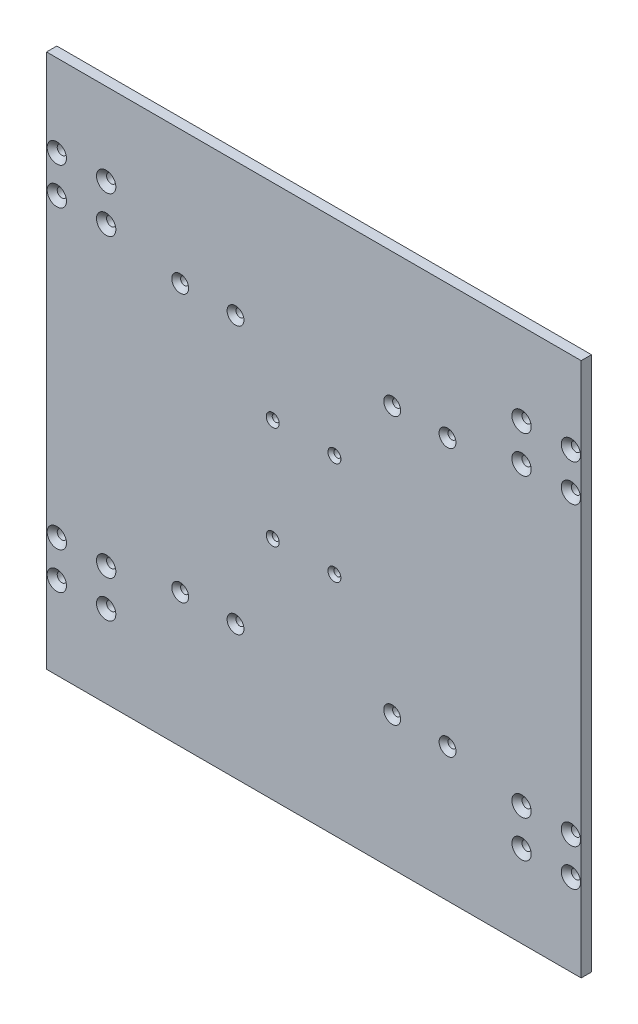
SolidWorks part; units mm, degrees
ref_plane "Front Plane" through (0, 0, 0) normal (0, 0, 1) x (1, 0, 0)
ref_plane "Top Plane" through (0, 0, 0) normal (0, 1, 0) x (1, 0, 0)
ref_plane "Right Plane" through (0, 0, 0) normal (1, 0, 0) x (0, 0, -1)
sketch "Sketch1" plane through (0, 0, 0) normal (0, 0, 1) x (1, 0, 0)
  line L1 (0, 0) -> (-260, 0)
  line L2 (0, 0) -> (0, 260)
  line L3 (0, 260) -> (-260, 260)
  line L4 (-260, 0) -> (-260, 260)
  dimension "D2" = 260
extrude "Boss-Extrude1" add sketch "Sketch1" along normal blind 5
sketch "Sketch3" plane through (0, 0, 0) normal (0, 0, -1) x (-1, 0, 0)
  line L0 (260, 260) -> (260, 0) construction
  line L1 (0, 260) -> (260, 260) construction
  circle A0 centre (135, 135) radius 1.5
  dimension "D1" = 3
  dimension "D3" = 125
  dimension "D2" = 125
extrude "temp. sensor" cut sketch "Sketch3" against normal blind 2
hole_wizard "CSK for M4 Flat Head Machine Screw1" positions "Sketch5" profile "Sketch4" countersink size "M4" standard "ANSI Metric" end condition through all
sketch "Sketch5" plane through (0, 0, 5) normal (0, 0, 1) x (1, 0, 0)
  line L0 (-260, 260) -> (-260, 0) construction
  line L1 (0, 260) -> (-260, 260) construction
  line L2 (-130, 260) -> (-130, 0) construction
  line L3 (-260, 0) -> (0, 0) construction
  line L5 (-260, 130) -> (0, 130) construction
  line L6 (0, 0) -> (0, 260) construction
  point P0 (-255, 220)
  point P2 (-231, 220)
  point P4 (-231, 202)
  point P6 (-255, 202)
  point P29 (-5, 202)
  point P30 (-29, 202)
  point P31 (-29, 220)
  point P32 (-5, 220)
  point P33 (-29, 58)
  point P34 (-5, 58)
  point P35 (-5, 40)
  point P36 (-29, 40)
  point P37 (-255, 40)
  point P38 (-231, 40)
  point P39 (-231, 58)
  point P40 (-255, 58)
  dimension "D1" = 5
  dimension "D2" = 24
  dimension "D3" = 40
  dimension "D4" = 18
sketch "Sketch4" plane through (-255, 220, 5) normal (1, 0, 0) x (0, -1, 0)
  line L0 (0, 0) -> (0, 5)
  line L1 (0, 5) -> (2.25, 5)
  line L2 (2.25, 5) -> (2.25, 2.45)
  line L3 (2.25, 2.45) -> (4.7, 0)
  line L5 (4.7, 0) -> (0, 0)
  line L6 (-2.25, 2.45) -> (-4.7, 0) construction
  line L11 (0, -6.35) -> (0, 107.95) construction
  dimension "Thru Hole Dia." = 4.5
  dimension "Thru Hole Depth" = 5
  dimension "Near C'Sink Dia." = 9.4
  dimension "Near C'Sink Angle" = 90
hole_wizard "CSK for M3.5 Flat Head Machine Screw1" positions "Sketch8" profile "Sketch7" countersink size "M3.5" standard "ANSI Metric" end condition through all
sketch "Sketch8" plane through (0, 0, 5) normal (0, 0, 1) x (1, 0, 0)
  line L0 (-260, 260) -> (-260, 0) construction
  line L1 (0, 260) -> (-260, 260) construction
  line L2 (-130, 260) -> (-130, 0) construction
  line L3 (-260, 0) -> (0, 0) construction
  line L5 (-260, 130) -> (0, 130) construction
  line L6 (0, 0) -> (0, 260) construction
  point P0 (-195, 195)
  point P2 (-168.093, 195)
  point P25 (-91.907, 195)
  point P26 (-65, 195)
  point P27 (-65, 65)
  point P28 (-91.907, 65)
  point P29 (-168.093, 65)
  point P30 (-195, 65)
  dimension "D1" = 65
  dimension "D2" = 65
  dimension "D3" = 26.907
sketch "Sketch7" plane through (-195, 195, 5) normal (1, 0, 0) x (0, -1, 0)
  line L0 (0, 0) -> (0, 5)
  line L1 (0, 5) -> (1.95, 5)
  line L2 (1.95, 5) -> (1.95, 2.15)
  line L3 (1.95, 2.15) -> (4.1, 0)
  line L5 (4.1, 0) -> (0, 0)
  line L6 (-1.95, 2.15) -> (-4.1, 0) construction
  line L11 (0, -6.35) -> (0, 107.95) construction
  dimension "Thru Hole Dia." = 3.9
  dimension "Thru Hole Depth" = 5
  dimension "Near C'Sink Dia." = 8.2
  dimension "Near C'Sink Angle" = 90
hole_wizard "CSK for M3 Flat Head Machine Screw1" positions "Sketch10" profile "Sketch9" countersink size "M3" standard "ANSI Metric" end condition through all
sketch "Sketch10" plane through (0, 0, 5) normal (0, 0, 1) x (1, 0, 0)
  line L0 (-260, 260) -> (-260, 0) construction
  line L1 (0, 260) -> (-260, 260) construction
  point P0 (-120, 110)
  point P2 (-150, 110)
  point P4 (-150, 160)
  point P6 (-120, 160)
  dimension "D1" = 30
  dimension "D2" = 110
  dimension "D3" = 50
  dimension "D4" = 100
sketch "Sketch9" plane through (-120, 110, 5) normal (1, 0, 0) x (0, -1, 0)
  line L0 (0, 0) -> (0, 5)
  line L1 (0, 5) -> (1.7, 5)
  line L2 (1.7, 5) -> (1.7, 1.45)
  line L3 (1.7, 1.45) -> (3.15, 0)
  line L5 (3.15, 0) -> (0, 0)
  line L6 (-1.7, 1.45) -> (-3.15, 0) construction
  line L11 (0, -6.35) -> (0, 107.95) construction
  dimension "Thru Hole Dia." = 3.4
  dimension "Thru Hole Depth" = 5
  dimension "Near C'Sink Dia." = 6.3
  dimension "Near C'Sink Angle" = 90
